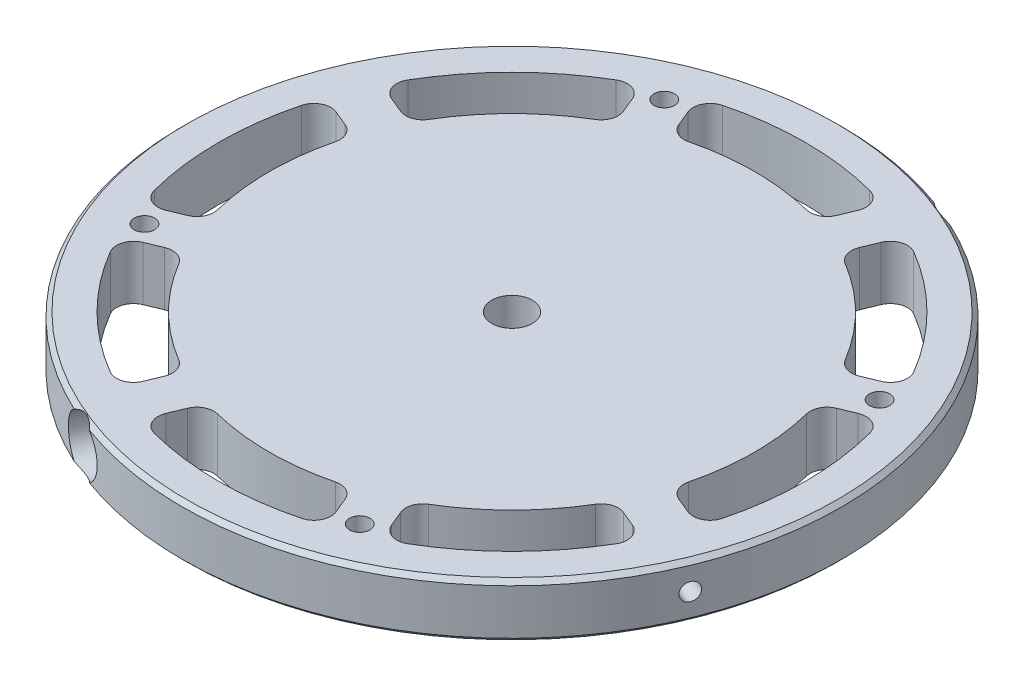
SolidWorks part; units mm, degrees
material "6061-T6 (SS)"
ref_plane "Front Plane" through (0, 0, 0) normal (0, 0, 1) x (1, 0, 0)
ref_plane "Top Plane" through (0, 0, 0) normal (0, 1, 0) x (1, 0, 0)
ref_plane "Right Plane" through (0, 0, 0) normal (1, 0, 0) x (0, 0, -1)
sketch "Sketch2" plane through (0, 0, 0) normal (1, 0, 0) x (0, 0, -1)
  line L0 (0, 0) -> (-77.55, 0)
  line L1 (-77.55, 0) -> (-77.55, 12.7)
  line L2 (-77.55, 12.7) -> (0, 12.7)
  line L5 (0, 12.7) -> (0, 0)
  dimension "D1" = 77.55
  dimension "D2" = 12.7
ref_axis "Axis1" through (0, -0.8888, 0) along (0, 1, 0)
revolve "Revolve1" add sketch "Sketch2" angle 360 about axis through (0, -0.8888, 0) along (0, 1, 0)
hole_wizard "#12 (0.189) Diameter Hole1" positions "Sketch6" profile "Sketch7" hole size "#12" standard "ANSI Inch" end condition through all
sketch "Sketch6" plane through (0, 12.7, 0) normal (0, 1, 0) x (1, 0, 0)
  line L0 (0, 0) -> (-53.438, 129.0108) construction
  line L2 (0, 0) -> (0, 109.0908) construction
  point P0 (-25.3336, 61.1608)
  dimension "D1" = 22.5
  dimension "D2" = 66.2
sketch "Sketch7" plane through (-25.3336, 12.7, -61.1608) normal (1, 0, 0) x (0, 0, 1)
  line L0 (0, 0) -> (0, 12.7)
  line L1 (0, 12.7) -> (2.4003, 12.7)
  line L2 (2.4003, 12.7) -> (2.4003, 0)
  line L5 (2.4003, 0) -> (0, 0)
  line L11 (0, -6.35) -> (0, 107.95) construction
  dimension "Thru Hole Dia." = 4.8006
  dimension "Thru Hole Depth" = 12.7
pattern_circular "CirPattern3" count 4 over 360 about axis through (0, 0, 0) along (0, 1, 0) of "#12 (0.189) Diameter Hole1"
sketch "Sketch8" plane through (0, 12.7, 0) normal (0, 1, 0) x (1, 0, 0)
  line L4 (0, 0) -> (0, 93.9995) construction
  line L5 (0, 0) -> (113.8372, 0) construction
  line L6 (-17.1671, 54.5107) -> (-21.7355, 65.5398)
  line L7 (17.1671, 54.5107) -> (21.7355, 65.5398)
  line L8 (0, 0) -> (-25.3336, 61.1608) construction
  arc A0 (-17.1671, 54.5107) -> (17.1671, 54.5107) centre (0, 0) cw
  arc A1 (-21.7355, 65.5398) -> (21.7355, 65.5398) centre (0, 0) cw
  circle A2 centre (0, 0) radius 77.55 construction
  dimension "D1" = 57.15
  dimension "D2" = 8.5
  dimension "D3" = 5
extrude "Cut-Extrude1" cut sketch "Sketch8" against normal through all
fillet "Fillet1" radius 4 4 edges at (17.1671, 6.35, -54.5107) (21.7355, 6.35, -65.5398) (-17.1671, 6.35, -54.5107) (-21.7355, 6.35, -65.5398)
pattern_circular "CirPattern4" count 8 over 360 about axis through (0, 0, 0) along (0, 1, 0) of "Cut-Extrude1", "Fillet1"
chamfer "Chamfer1" distance 1 angle 45 2 edges at (0, 0, -77.55) (0, 12.7, -77.55)
ref_plane "Plane1" through (0, 0, 0) normal (0.9239, 0, 0.3827) x (0, 1, 0)
hole_wizard "#20 (0.161) Diameter Hole1" positions "Sketch16" profile "Sketch15" hole size "#20" standard "ANSI Inch"
sketch "Sketch16" plane through (0, 0, 0) normal (0.9239, 0, 0.3827) x (0, 1, 0)
  point P0 (6.35, 0)
  dimension "D1" = 6.35
sketch "Sketch15" plane through (0, 6.35, 0) normal (0, 1, 0) x (-0.3827, 0, 0.9239)
  line L0 (0, 0) -> (0, 101.324)
  line L1 (0, 101.324) -> (2.0447, 101.324)
  line L2 (2.0447, 101.324) -> (2.0447, 0)
  line L5 (2.0447, 0) -> (0, 0)
  line L11 (0, -6.35) -> (0, 107.95) construction
  dimension "Thru Hole Dia." = 4.0894
  dimension "Thru Hole Depth" = 101.324
ref_plane "Plane2" through (29.6771, 0, -71.6469) normal (0.3827, 0, -0.9239) x (-0.9239, 0, -0.3827)
sketch "Sketch19" plane through (29.6771, 0, -71.6469) normal (0.3827, 0, -0.9239) x (-0.9239, 0, -0.3827)
  line L0 (-76.55, 0) -> (76.55, 0) construction
  line L2 (0, -0.8888) -> (0, 13.5888) construction
  circle A0 centre (0, 6.35) radius 5.5625 construction
  circle A1 centre (0, 6.35) radius 6.25
  dimension "D1" = 12.5
  dimension "D2" = 6.35
extrude "Cut-Extrude3" cut sketch "Sketch19" against normal blind 5
pattern_circular "CirPattern5" count 2 over 360 about axis through (0, -0.8888, 0) along (0, 1, 0) of "Cut-Extrude3"
hole_wizard "#10-24 Tapped Hole1" positions "Sketch20" profile "Sketch21" tap size "#10-24" standard "ANSI Inch"
sketch "Sketch20" plane through (-27.7637, 0, 67.0275) normal (-0.3827, 0, 0.9239) x (0.9239, 0, 0.3827)
  circle A0 centre (0, 6.35) radius 6.25
  circle A1 centre (0, 6.35) radius 6.25 construction
  point P0 (0, 6.35)
sketch "Sketch21" plane through (-27.7637, 6.35, 67.0275) normal (0, 1, 0) x (0.9239, 0, 0.3827)
  line L0 (0, 0) -> (0, 51.9408)
  line L1 (0, 51.9408) -> (1.8986, 50.8)
  line L2 (1.8986, 50.8) -> (1.8986, 0)
  line L5 (1.8986, 0) -> (0, 0)
  line L10 (0, 51.9408) -> (-1.8986, 50.8) construction
  line L11 (0, -6.35) -> (0, 107.95) construction
  dimension "Tap Drill Dia." = 3.7973
  dimension "Tap Drill Depth" = 50.8
  dimension "Drill Angle" = 118
pattern_circular "CirPattern6" count 2 over 360 about axis through (0, -0.8888, 0) along (0, 1, 0) of "#10-24 Tapped Hole1"
sketch "Sketch22" plane through (0, 12.7, 0) normal (0, 1, 0) x (1, 0, 0)
  circle A0 centre (0, 0) radius 4.765
  dimension "D1" = 9.53
extrude "Cut-Extrude4" cut sketch "Sketch22" against normal blind 12.8
equation "\"TubeDiameter\"= 6.500in"
equation "\"D1@Sketch2\"=(\"TubeDiameter\"/2)-5mm"
equation "\"D2@Sketch6\"=66.2"
